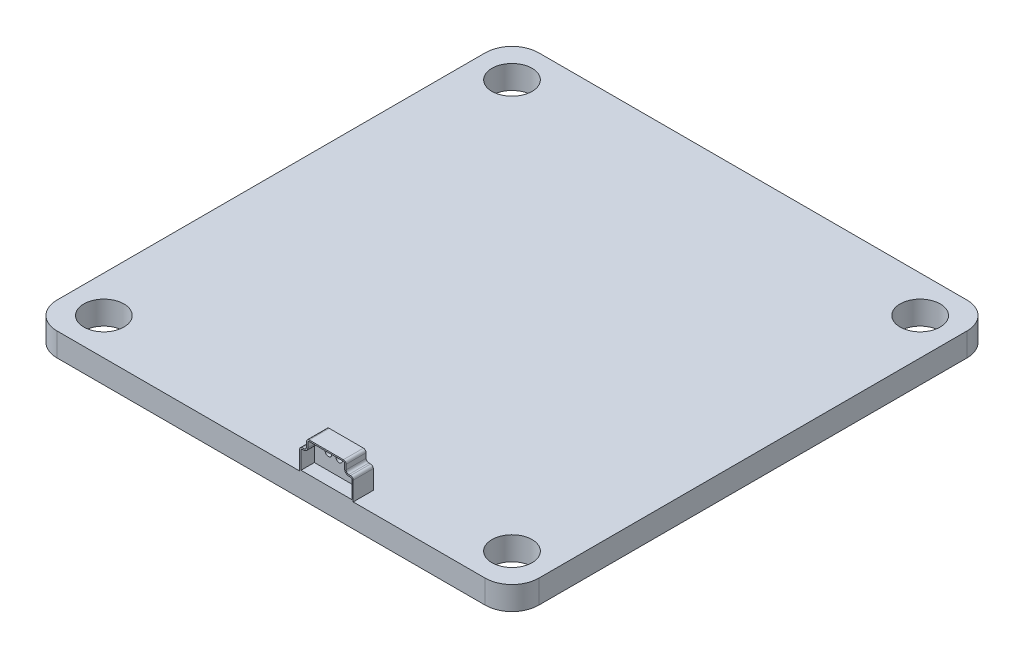
SolidWorks part; units mm, degrees
ref_plane "Front Plane" through (0, 0, 0) normal (0, 0, 1) x (1, 0, 0)
ref_plane "Top Plane" through (0, 0, 0) normal (0, 1, 0) x (1, 0, 0)
ref_plane "Right Plane" through (0, 0, 0) normal (1, 0, 0) x (0, 0, -1)
sketch "Sketch1" plane through (0, 0, 0) normal (0, 1, 0) x (1, 0, 0)
  line L1 (-16, 18) -> (16, 18)
  line L2 (-18, 16) -> (-18, -16)
  line L3 (-16, -18) -> (16, -18)
  line L4 (18, 16) -> (18, -16)
  line L5 (-18, 18) -> (18, -18) construction
  line L6 (-18, -18) -> (18, 18) construction
  line L7 (-15.25, 15.25) -> (15.25, 15.25) construction
  line L8 (-15.25, 15.25) -> (-15.25, -15.25) construction
  line L9 (-15.25, -15.25) -> (15.25, -15.25) construction
  line L10 (15.25, 15.25) -> (15.25, -15.25) construction
  line L11 (-15.25, 15.25) -> (15.25, -15.25) construction
  line L12 (-15.25, -15.25) -> (15.25, 15.25) construction
  circle A0 centre (-15.25, 15.25) radius 1.5
  circle A1 centre (15.25, 15.25) radius 1.5
  circle A2 centre (-15.25, -15.25) radius 1.5
  circle A3 centre (15.25, -15.25) radius 1.5
  arc A4 (-16, 18) -> (-18, 16) centre (-16, 16) ccw
  arc A5 (16, 18) -> (18, 16) centre (16, 16) cw
  arc A6 (16, -18) -> (18, -16) centre (16, -16) ccw
  arc A7 (-18, -16) -> (-16, -18) centre (-16, -16) ccw
  point P0 (0, 0)
  point P6 (0, 0)
  dimension "D4" = 3
  dimension "D5" = 2
  dimension "D1" = 36
  dimension "D2" = 36
  dimension "D3" = 30.5
extrude "Boss-Extrude1" add sketch "Sketch1" along normal blind 1.75
sketch "Sketch2" plane through (0, 0, 18) normal (0, 0, 1) x (1, 0, 0)
  line L0 (-16, 1.75) -> (16, 1.75) construction
  line L1 (2.8435, 4.1167) -> (5.3987, 4.1167)
  line L2 (2.1337, 3.1556) -> (2.1337, 1.75)
  line L3 (2.1337, 1.75) -> (6.1337, 1.75)
  line L4 (6.1337, 3.1556) -> (6.1337, 1.75)
  line L5 (2.3337, 3.3556) -> (2.4435, 3.3556)
  line L6 (2.6435, 3.5556) -> (2.6435, 3.9167)
  line L7 (5.5987, 3.9167) -> (5.5987, 3.5556)
  line L8 (5.7987, 3.3556) -> (5.9337, 3.3556)
  line L9 (2.8435, 4.0167) -> (5.3987, 4.0167)
  line L10 (5.4987, 3.9167) -> (5.4987, 3.5556)
  line L11 (5.7987, 3.2556) -> (5.9337, 3.2556)
  line L12 (6.0337, 3.1556) -> (6.0337, 1.85)
  line L13 (2.2337, 1.85) -> (6.0337, 1.85)
  line L14 (2.2337, 3.1556) -> (2.2337, 1.85)
  line L15 (2.3337, 3.2556) -> (2.4435, 3.2556)
  line L16 (2.7435, 3.5556) -> (2.7435, 3.9167)
  arc A0 (5.3987, 4.1167) -> (5.5987, 3.9167) centre (5.3987, 3.9167) cw
  arc A1 (5.9337, 3.3556) -> (6.1337, 3.1556) centre (5.9337, 3.1556) cw
  arc A2 (2.3337, 3.3556) -> (2.1337, 3.1556) centre (2.3337, 3.1556) ccw
  arc A3 (2.4435, 3.3556) -> (2.6435, 3.5556) centre (2.4435, 3.5556) ccw
  arc A4 (2.6435, 3.9167) -> (2.8435, 4.1167) centre (2.8435, 3.9167) cw
  arc A5 (5.5987, 3.5556) -> (5.7987, 3.3556) centre (5.7987, 3.5556) ccw
  arc A6 (5.3987, 4.0167) -> (5.4987, 3.9167) centre (5.3987, 3.9167) cw
  arc A7 (5.4987, 3.5556) -> (5.7987, 3.2556) centre (5.7987, 3.5556) ccw
  arc A8 (5.9337, 3.2556) -> (6.0337, 3.1556) centre (5.9337, 3.1556) cw
  arc A9 (2.3337, 3.2556) -> (2.2337, 3.1556) centre (2.3337, 3.1556) ccw
  arc A10 (2.4435, 3.2556) -> (2.7435, 3.5556) centre (2.4435, 3.5556) ccw
  arc A11 (2.7435, 3.9167) -> (2.8435, 4.0167) centre (2.8435, 3.9167) cw
  point P18 (2.6435, 3.9645)
  point P21 (5.4845, 3.343)
  point P22 (5.5987, 3.3556)
  dimension "D1" = 0.2
  dimension "D2" = 0.2
  dimension "D3" = 0.2
  dimension "D4" = 0.1
extrude "Boss-Extrude6" add sketch "Sketch2" against normal blind 1
sketch "Sketch6" plane through (0, 0, 17) normal (0, 0, -1) x (-1, 0, 0)
  line L8 (-5.5987, 3.9167) -> (-5.5987, 3.5556)
  line L9 (-5.7987, 3.3556) -> (-5.9337, 3.3556)
  line L10 (-6.1337, 3.1556) -> (-6.1337, 1.75)
  line L11 (-6.1337, 1.75) -> (-2.1337, 1.75)
  line L12 (-2.1337, 1.75) -> (-2.1337, 3.1556)
  line L13 (-2.3337, 3.3556) -> (-2.4435, 3.3556)
  line L14 (-2.6435, 3.5556) -> (-2.6435, 3.9167)
  line L15 (-2.8435, 4.1167) -> (-5.3987, 4.1167)
  line L16 (-5.5987, 3.9167) -> (-5.5987, 3.5556)
  line L17 (-5.7987, 3.3556) -> (-5.9337, 3.3556)
  line L18 (-6.1337, 3.1556) -> (-6.1337, 1.75)
  line L19 (-6.1337, 1.75) -> (-2.1337, 1.75)
  line L20 (-2.1337, 1.75) -> (-2.1337, 3.1556)
  line L21 (-2.3337, 3.3556) -> (-2.4435, 3.3556)
  line L22 (-2.6435, 3.5556) -> (-2.6435, 3.9167)
  line L23 (-2.8435, 4.1167) -> (-5.3987, 4.1167)
  arc A6 (-5.3987, 4.1167) -> (-5.5987, 3.9167) centre (-5.3987, 3.9167) ccw
  arc A7 (-5.7987, 3.3556) -> (-5.5987, 3.5556) centre (-5.7987, 3.5556) ccw
  arc A8 (-5.9337, 3.3556) -> (-6.1337, 3.1556) centre (-5.9337, 3.1556) ccw
  arc A9 (-2.1337, 3.1556) -> (-2.3337, 3.3556) centre (-2.3337, 3.1556) ccw
  arc A10 (-2.6435, 3.5556) -> (-2.4435, 3.3556) centre (-2.4435, 3.5556) ccw
  arc A11 (-2.6435, 3.9167) -> (-2.8435, 4.1167) centre (-2.8435, 3.9167) ccw
  arc A12 (-5.3987, 4.1167) -> (-5.5987, 3.9167) centre (-5.3987, 3.9167) ccw
  arc A13 (-5.7987, 3.3556) -> (-5.5987, 3.5556) centre (-5.7987, 3.5556) ccw
  arc A14 (-5.9337, 3.3556) -> (-6.1337, 3.1556) centre (-5.9337, 3.1556) ccw
  arc A15 (-2.1337, 3.1556) -> (-2.3337, 3.3556) centre (-2.3337, 3.1556) ccw
  arc A16 (-2.6435, 3.5556) -> (-2.4435, 3.3556) centre (-2.4435, 3.5556) ccw
  arc A17 (-2.6435, 3.9167) -> (-2.8435, 4.1167) centre (-2.8435, 3.9167) ccw
  dimension "D1" = 0
extrude "Boss-Extrude7" add sketch "Sketch6" along normal blind 0.5
sketch "Sketch7" plane through (0, 0, 16.5) normal (0, 0, -1) x (-1, 0, 0)
  line L0 (-4.8781, 3.0169) -> (-3.2781, 3.01) construction
  circle A0 centre (-4.8781, 3.0169) radius 0.25
  circle A1 centre (-4.0781, 3.0136) radius 0.25
  circle A2 centre (-3.2781, 3.01) radius 0.25
  point P6 (-4.3297, 3.0169)
  point P7 (-3.2781, 3.0136)
  point P8 (0, 0)
  dimension "D1" = 0.5
  dimension "D2" = 0.8
  dimension "D3" = 0.8
extrude "Cut-Extrude1" cut sketch "Sketch7" against normal up to next
